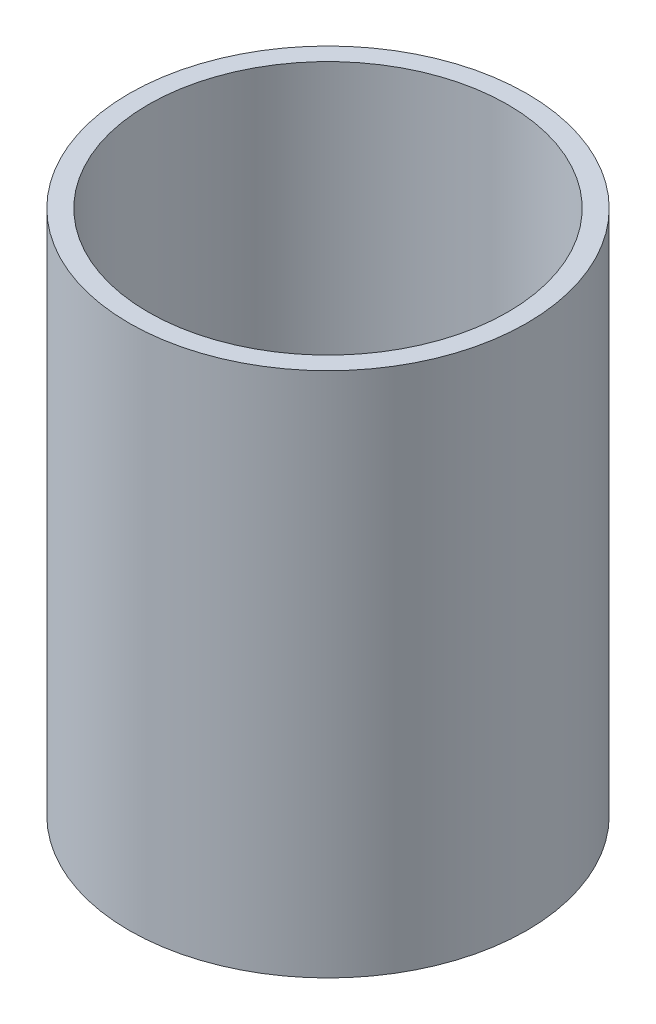
SolidWorks part; units mm, degrees
ref_plane "Plan de face" through (0, 0, 0) normal (0, 0, 1) x (1, 0, 0)
ref_plane "Plan de dessus" through (0, 0, 0) normal (0, 1, 0) x (1, 0, 0)
ref_plane "Plan de droite" through (0, 0, 0) normal (1, 0, 0) x (0, 0, -1)
sketch "Esquisse1" plane through (0, 0, 0) normal (0, 1, 0) x (1, 0, 0)
  circle A0 centre (0, 0) radius 25
  circle A1 centre (0, 0) radius 22.6
  dimension "D1" = 50
  dimension "D2" = 45.2
extrude "Boss.-Extru.1" add sketch "Esquisse1" along normal mid plane 66.12
